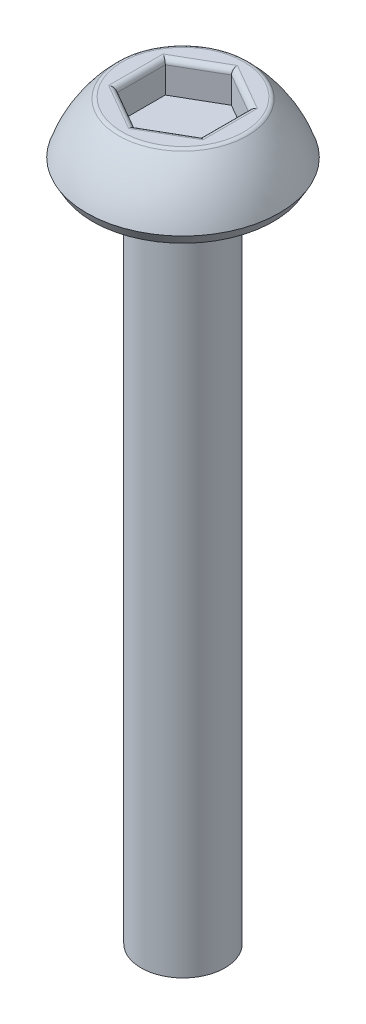
SolidWorks part; units mm, degrees
ref_plane "Front Plane" through (0, 0, 0) normal (0, 0, 1) x (1, 0, 0)
ref_plane "Top Plane" through (0, 0, 0) normal (0, 1, 0) x (1, 0, 0)
ref_plane "Right Plane" through (0, 0, 0) normal (1, 0, 0) x (0, 0, -1)
sketch "Sketch1" plane through (0, 0, 0) normal (1, 0, 0) x (0, 0, -1)
  line L0 (0, 0) -> (0, 1.5) construction
  line L1 (0, 1.5) -> (-1.5, 1.5)
  line L3 (-2.3, 0.25) -> (-2.1557, 0)
  line L4 (-2.1557, 0) -> (-1, 0)
  line L5 (-1, 0) -> (-1, -16)
  line L6 (-1, -16) -> (0, -16)
  line L7 (0, -16) -> (0, 1.5)
  line L8 (0, 0) -> (-1, 0) construction
  arc A0 (-1.5, 1.5) -> (-2.3, 0.25) centre (0.5483, -0.6919) ccw
  dimension "D5" = 3
  dimension "D1" = 1.5
  dimension "D2" = 2.3
  dimension "D3" = 1.5
  dimension "D4" = 0.25
  dimension "D6" = 60
  dimension "D7" = 1
  dimension "D8" = 16
  dimension "D9" = 2.3
revolve "Revolve1" add sketch "Sketch1" angle 360 about L7
sketch "Sketch2" plane through (0, 1.5, 0) normal (0, 1, 0) x (1, 0, 0)
  line L1 (0, 1.1547) -> (-1, 0.5774)
  line L2 (-1, 0.5774) -> (-1, -0.5774)
  line L3 (-1, -0.5774) -> (0, -1.1547)
  line L4 (0, -1.1547) -> (1, -0.5774)
  line L5 (1, -0.5774) -> (1, 0.5774)
  line L6 (1, 0.5774) -> (0, 1.1547)
  circle A0 centre (0, 0) radius 1 construction
  dimension "D1" = 2
extrude "Cut-Extrude1" cut sketch "Sketch2" against normal blind 0.75
fillet "Fillet1" radius 0.125 7 edges at (0, 1.5, -1.5) (-0.5, 1.5, 0.866) (0.5, 1.5, 0.866) (1, 1.5, 0) (0.5, 1.5, -0.866) (-0.5, 1.5, -0.866) (-1, 1.5, 0)
